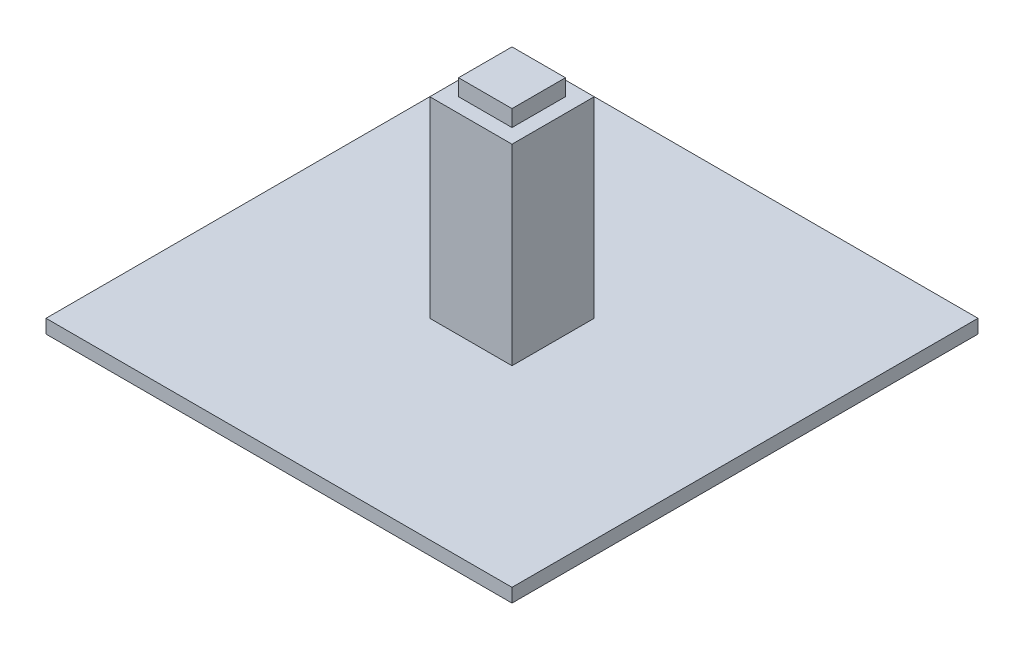
SolidWorks part; units mm, degrees
ref_plane "Front Plane" through (0, 0, 0) normal (0, 0, 1) x (1, 0, 0)
ref_plane "Top Plane" through (0, 0, 0) normal (0, 1, 0) x (1, 0, 0)
ref_plane "Right Plane" through (0, 0, 0) normal (1, 0, 0) x (0, 0, -1)
sketch "Sketch1" plane through (0, 0, 0) normal (0, 1, 0) x (1, 0, 0)
  line L1 (-85, -85) -> (85, -85)
  line L2 (-85, -85) -> (-85, 85)
  line L3 (-85, 85) -> (85, 85)
  line L4 (85, -85) -> (85, 85)
  line L5 (-85, -85) -> (85, 85) construction
  line L6 (-85, 85) -> (85, -85) construction
  point P0 (0, 0)
  dimension "D1" = 170
  dimension "D2" = 170
extrude "Boss-Extrude1" add sketch "Sketch1" along normal blind 5
sketch "Sketch2" plane through (0, 5, 0) normal (0, 1, 0) x (1, 0, 0)
  line L1 (-15, -15) -> (15, -15)
  line L2 (-15, -15) -> (-15, 15)
  line L3 (-15, 15) -> (15, 15)
  line L4 (15, -15) -> (15, 15)
  line L5 (-15, -15) -> (15, 15) construction
  line L6 (-15, 15) -> (15, -15) construction
  point P0 (0, 0)
  dimension "D1" = 30
  dimension "D2" = 30
extrude "Boss-Extrude2" add sketch "Sketch2" along normal blind 70
sketch "Sketch3" plane through (0, 75, 0) normal (0, 1, 0) x (1, 0, 0)
  line L1 (-9.75, -9.75) -> (9.75, -9.75)
  line L2 (-9.75, -9.75) -> (-9.75, 9.75)
  line L3 (-9.75, 9.75) -> (9.75, 9.75)
  line L4 (9.75, -9.75) -> (9.75, 9.75)
  line L5 (-9.75, -9.75) -> (9.75, 9.75) construction
  line L6 (-9.75, 9.75) -> (9.75, -9.75) construction
  point P0 (0, 0)
  dimension "D1" = 19.5
  dimension "D2" = 19.5
extrude "Boss-Extrude3" add sketch "Sketch3" along normal blind 6
